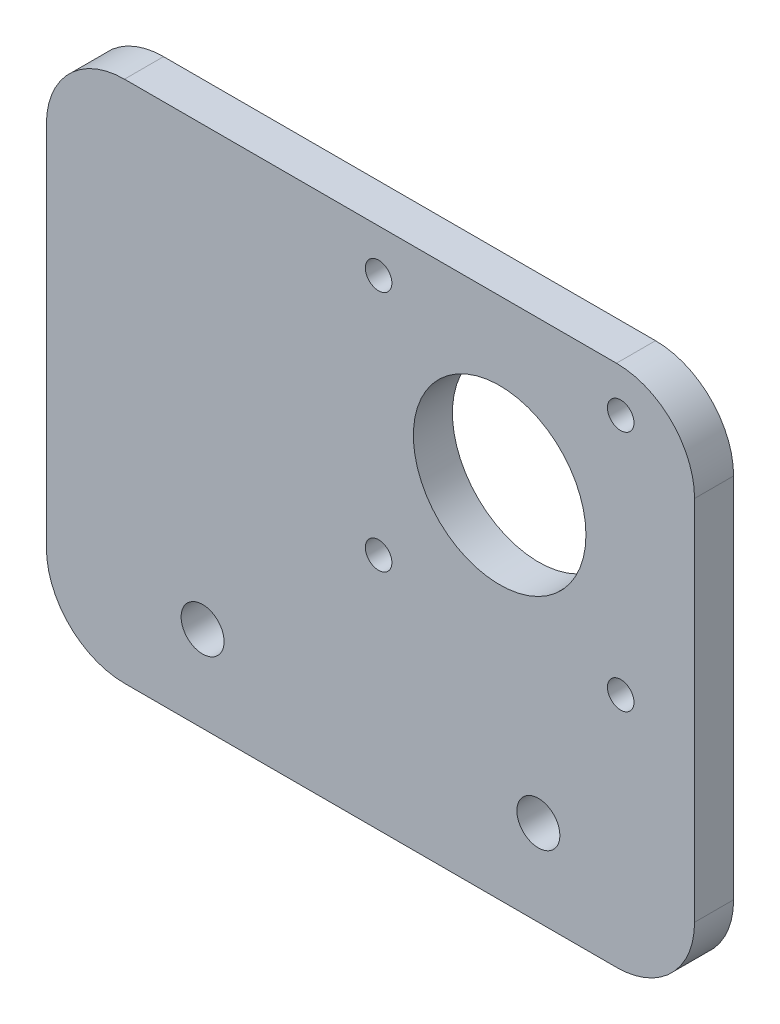
SolidWorks part; units mm, degrees
ref_plane "Front Plane" through (0, 0, 0) normal (0, 0, 1) x (1, 0, 0)
ref_plane "Top Plane" through (0, 0, 0) normal (0, 1, 0) x (1, 0, 0)
ref_plane "Right Plane" through (0, 0, 0) normal (1, 0, 0) x (0, 0, -1)
sketch "Sketch1" plane through (0, 0, 0) normal (0, 0, 1) x (1, 0, 0)
  line L0 (0, 0) -> (0, -22.5) construction
  line L1 (-41.5, -33.5) -> (41.5, -33.5)
  line L2 (-41.5, -33.5) -> (-41.5, 33.5)
  line L3 (-41.5, 33.5) -> (41.5, 33.5)
  line L4 (41.5, -33.5) -> (41.5, 33.5)
  line L5 (-41.5, -33.5) -> (41.5, 33.5) construction
  line L6 (-41.5, 33.5) -> (41.5, -33.5) construction
  line L7 (0, -22.5) -> (21.5, -22.5) construction
  point P0 (0, 0)
  point P9 (41.5, 27.5574)
  dimension "D1" = 21.5
  dimension "D2" = 11
  dimension "D3" = 83
  dimension "D4" = 67
extrude "Boss-Extrude1" add sketch "Sketch1" along normal blind 5
hole_wizard "M5 Clearance Hole1" positions "Sketch2" profile "Sketch3" hole size "M5" standard "ISO" end condition through all
sketch "Sketch2" plane through (0, 0, 5) normal (0, 0, 1) x (1, 0, 0)
  line L0 (-21.5, -22.5) -> (21.5, -22.5) construction
  line L2 (0, -22.5) -> (0, 0) construction
  line L4 (-41.5, -33.5) -> (41.5, -33.5) construction
  point P0 (21.5, -22.5)
  point P3 (-21.5, -22.5)
  dimension "D1" = 43
  dimension "D2" = 11
sketch "Sketch3" plane through (21.5, -22.5, 5) normal (1, 0, 0) x (0, -1, 0)
  line L0 (0, 0) -> (0, 5)
  line L1 (0, 5) -> (2.75, 5)
  line L2 (2.75, 5) -> (2.75, 0)
  line L5 (2.75, 0) -> (0, 0)
  line L11 (0, -6.35) -> (0, 107.95) construction
  dimension "Thru Hole Dia." = 5.5
  dimension "Thru Hole Depth" = 5
hole_wizard "M3 Clearance Hole1" positions "Sketch4" profile "Sketch5" hole size "M3" standard "ISO" end condition through all
sketch "Sketch4" plane through (0, 0, 0) normal (0, 0, -1) x (-1, 0, 0)
  circle A0 centre (-1.0411, -3) radius 1.5 construction
  point P0 (-32.0411, 28)
  point P3 (-1.0411, 28)
  point P6 (-1.0411, -3)
  point P8 (-32.0411, -3)
  point P12 (0, 0)
sketch "Sketch5" plane through (32.0411, 28, 0) normal (1, 0, 0) x (0, 1, 0)
  line L0 (0, 0) -> (0, 5)
  line L1 (0, 5) -> (1.7, 5)
  line L2 (1.7, 5) -> (1.7, 0)
  line L5 (1.7, 0) -> (0, 0)
  line L11 (0, -6.35) -> (0, 107.95) construction
  dimension "Thru Hole Dia." = 3.4
  dimension "Thru Hole Depth" = 5
sketch "Sketch6" plane through (0, 0, 5) normal (0, 0, 1) x (1, 0, 0)
  circle A0 centre (16.5411, 12.5) radius 11.05
  point P2 (0, 0)
  point P3 (16.5411, 12.5)
  dimension "D1" = 22.1
extrude "Cut-Extrude1" cut sketch "Sketch6" against normal through all
fillet "Fillet1" radius 10 4 edges at (41.5, -33.5, 2.5) (-41.5, -33.5, 2.5) (-41.5, 33.5, 2.5) (41.5, 33.5, 2.5)
